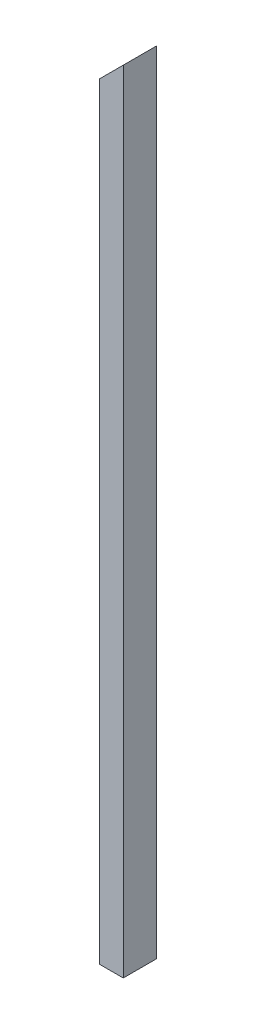
SolidWorks part; units mm, degrees
material "1023 Carbon Steel Sheet (SS)"
ref_plane "Front Plane" through (0, 0, 0) normal (0, 0, 1) x (1, 0, 0)
ref_plane "Top Plane" through (0, 0, 0) normal (0, 1, 0) x (1, 0, 0)
ref_plane "Right Plane" through (0, 0, 0) normal (1, 0, 0) x (0, 0, -1)
sketch "Sketch3" plane through (0, 0, 0) normal (0, 0, 1) x (1, 0, 0)
  line L0 (0, 0) -> (0, 2057.4)
  line L1 (0, 2057.4) -> (63.5, 2120.9)
  line L2 (63.5, 0) -> (63.5, 2120.9)
  line L3 (63.5, 0) -> (0, 0)
  dimension "D1" = 2057.4
  dimension "D2" = 63.5
  dimension "D3" = 135
extrude "Boss-Extrude1" add sketch "Sketch3" along normal blind 88.9
